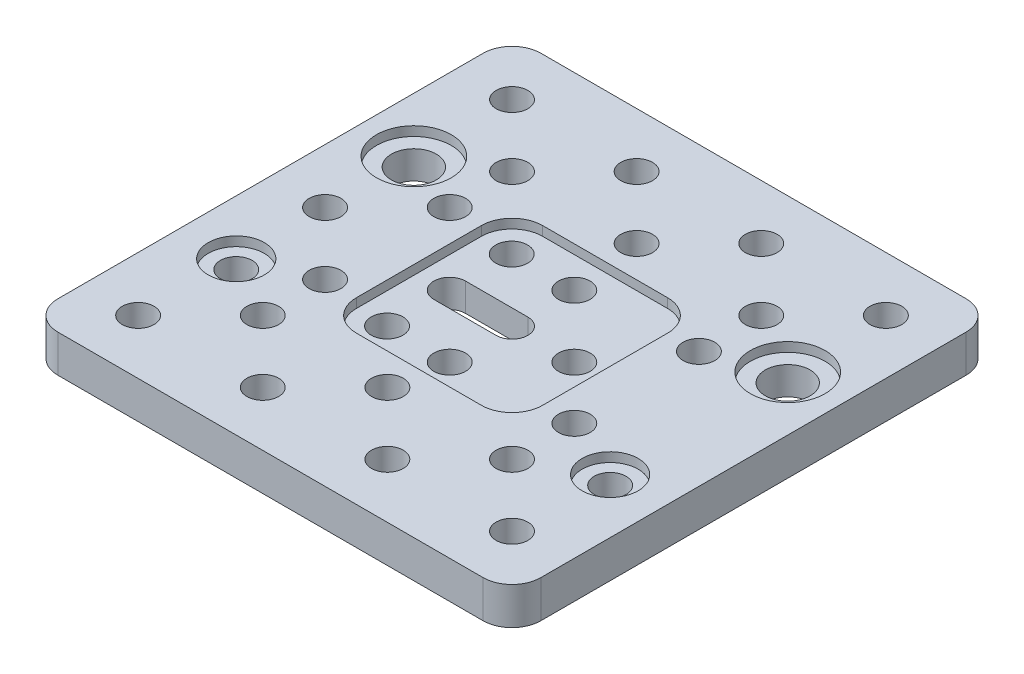
SolidWorks part; units mm, degrees
ref_plane "Front" through (0, 0, 0) normal (0, 0, 1) x (1, 0, 0)
ref_plane "Top" through (0, 0, 0) normal (0, 1, 0) x (1, 0, 0)
ref_plane "Right" through (0, 0, 0) normal (1, 0, 0) x (0, 0, -1)
sketch "Sketch1" plane through (0, 0, 0) normal (0, 1, 0) x (1, 0, 0)
  line L0 (0, 77.519) -> (0, 0) construction
  line L1 (-34.12, 0) -> (34.12, 0)
  line L2 (-38.755, 4.635) -> (-38.755, 72.884)
  line L3 (-34.12, 77.519) -> (34.12, 77.519)
  line L4 (38.755, 4.635) -> (38.755, 72.884)
  line L5 (-38.755, 68.76) -> (38.755, 68.76) construction
  line L6 (-38.755, 38.7595) -> (38.755, 38.7595) construction
  line L7 (-38.755, 58.76) -> (38.755, 58.76) construction
  line L8 (-38.755, 48.7595) -> (38.755, 48.7595) construction
  line L9 (0, 38.7595) -> (-10, 38.7595) construction
  line L10 (0, 36.2095) -> (-10, 36.2095)
  line L11 (0, 41.3095) -> (-10, 41.3095)
  line L12 (-30, 8.759) -> (-30, 68.76) construction
  arc A0 (-38.755, 4.635) -> (-34.12, 0) centre (-34.12, 4.635) ccw
  arc A1 (34.12, 0) -> (38.755, 4.635) centre (34.12, 4.635) ccw
  arc A2 (38.755, 72.884) -> (34.12, 77.519) centre (34.12, 72.884) ccw
  arc A3 (-34.12, 77.519) -> (-38.755, 72.884) centre (-34.12, 72.884) ccw
  circle A4 centre (-10, 68.76) radius 2.55
  circle A5 centre (-30, 68.76) radius 2.55
  circle A6 centre (10, 68.76) radius 2.55
  circle A7 centre (30, 68.76) radius 2.55
  circle A8 centre (-30, 8.759) radius 2.55
  circle A9 centre (-10, 8.759) radius 2.55
  circle A10 centre (10, 8.759) radius 2.55
  circle A11 centre (30, 8.759) radius 2.55
  circle A12 centre (0, 58.76) radius 2.55
  circle A13 centre (-20, 58.76) radius 2.55
  circle A14 centre (20, 58.76) radius 2.55
  circle A15 centre (20, 18.759) radius 2.55
  circle A16 centre (0, 18.759) radius 2.55
  circle A17 centre (-20, 18.759) radius 2.55
  circle A18 centre (-20, 48.7595) radius 2.55
  circle A19 centre (0, 48.7595) radius 2.55
  circle A20 centre (20, 48.7595) radius 2.55
  circle A21 centre (-10.05, 48.7595) radius 2.55
  circle A22 centre (20, 28.7595) radius 2.55
  circle A23 centre (0, 28.7595) radius 2.55
  circle A24 centre (-10.05, 28.7595) radius 2.55
  circle A25 centre (-20, 28.7595) radius 2.55
  circle A26 centre (10, 38.7595) radius 2.55
  arc A27 (0, 36.2095) -> (0, 41.3095) centre (0, 38.7595) ccw
  arc A28 (-10, 41.3095) -> (-10, 36.2095) centre (-10, 38.7595) ccw
  circle A29 centre (-30, 38.7595) radius 2.55
  circle A30 centre (-30, 53.01) radius 3.6
  circle A31 centre (-30, 24.509) radius 2.55
  circle A32 centre (30, 24.509) radius 2.55
  circle A33 centre (30, 53.01) radius 3.6
  point P71 (-5, 38.7595)
  dimension "D1" = 4.635
  dimension "D5" = 5.1
  dimension "D14" = 7.2
  dimension "D2" = 77.519
  dimension "D3" = 77.51
  dimension "D4" = 20
  dimension "D6" = 20
  dimension "D7" = 68.76
  dimension "D8" = 58.76
  dimension "D9" = 20
  dimension "D10" = 20
  dimension "D11" = 10.05
  dimension "D12" = 10
  dimension "D13" = 10
  dimension "D15" = 15.75
  dimension "D16" = 15.75
extrude "Boss-Extrude1" add sketch "Sketch1" along normal blind 6
sketch "Sketch2" plane through (0, 6, 0) normal (0, 1, 0) x (1, 0, 0)
  line L0 (0, 77.519) -> (0, 0) construction
  line L1 (34.12, 77.519) -> (-34.12, 77.519) construction
  line L2 (-38.755, 38.7595) -> (38.755, 38.7595) construction
  line L3 (-10.03, 53.7095) -> (10.03, 53.7095)
  line L4 (-14.951, 48.7885) -> (-14.951, 28.7305)
  line L5 (-10.03, 23.8095) -> (10.03, 23.8095)
  line L6 (14.951, 48.7885) -> (14.951, 28.7305)
  line L7 (-38.755, 72.884) -> (-38.755, 4.635) construction
  line L8 (38.755, 4.635) -> (38.755, 72.884) construction
  circle A0 centre (-30, 53.01) radius 6
  circle A1 centre (-30, 24.509) radius 4.5
  circle A2 centre (30, 53.01) radius 6
  circle A3 centre (30, 24.509) radius 4.5
  arc A4 (-10.03, 53.7095) -> (-14.951, 48.7885) centre (-10.03, 48.7885) ccw
  arc A5 (14.951, 48.7885) -> (10.03, 53.7095) centre (10.03, 48.7885) ccw
  arc A6 (10.03, 23.8095) -> (14.951, 28.7305) centre (10.03, 28.7305) ccw
  arc A7 (-14.951, 28.7305) -> (-10.03, 23.8095) centre (-10.03, 28.7305) ccw
  point P33 (14.951, 38.7595)
  point P34 (0, 23.8095)
  dimension "D1" = 12
  dimension "D2" = 9
  dimension "D3" = 4.921
  dimension "D4" = 29.902
  dimension "D5" = 29.9
extrude "Cut-Extrude1" cut sketch "Sketch2" against normal blind 1.5
